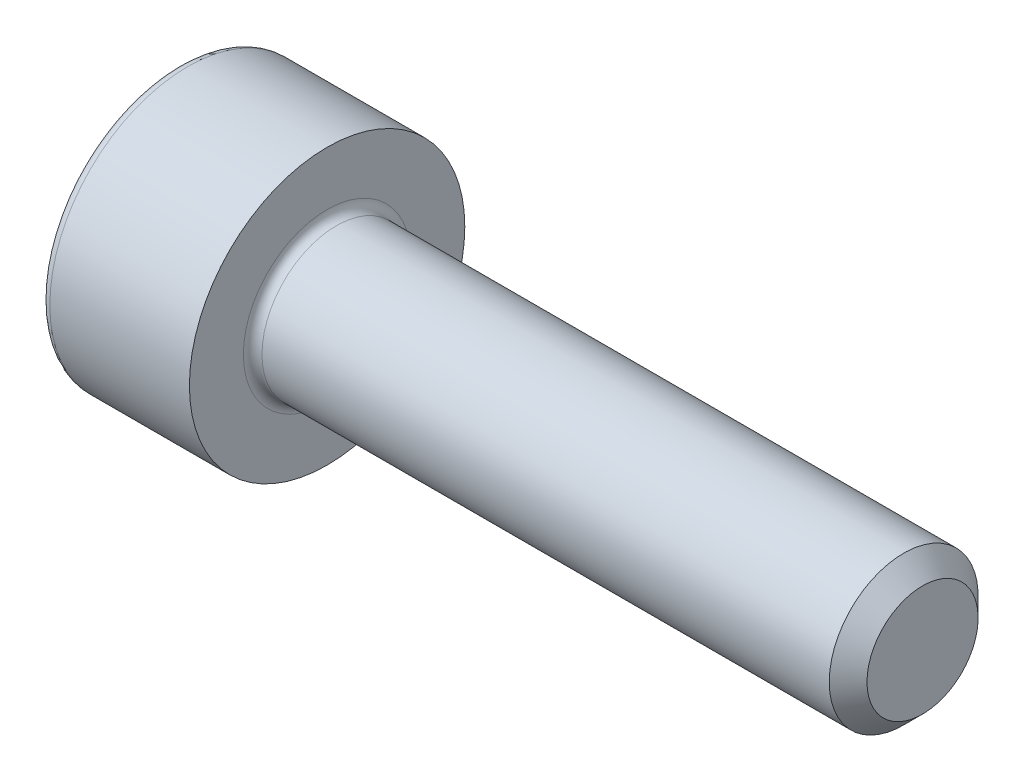
SolidWorks part; units mm, degrees
ref_plane "Front" through (0, 0, 0) normal (0, 0, 1) x (1, 0, 0)
ref_plane "Top" through (0, 0, 0) normal (0, 1, 0) x (1, 0, 0)
ref_plane "Right" through (0, 0, 0) normal (1, 0, 0) x (0, 0, -1)
sketch "Sketch1" plane through (0, 0, 0) normal (0, 0, 1) x (1, 0, 0)
  line L0 (7.7465, 1) -> (0.125, 1)
  line L1 (-2, 1.725) -> (-2, 0)
  line L2 (0, 1.85) -> (-1.875, 1.85)
  line L3 (0, 1.125) -> (0, 1.85)
  line L4 (8, 0.7465) -> (8, 0)
  line L5 (8, 0.7465) -> (7.7465, 1)
  line L6 (-2, 0) -> (0, 0) construction
  line L7 (-2, 0) -> (8, 0)
  arc A0 (-1.875, 1.85) -> (-2, 1.725) centre (-1.875, 1.725) ccw
  arc A1 (0, 1.125) -> (0.125, 1) centre (0.125, 1.125) ccw
  point P12 (0, 1.4875)
  dimension "D5" = 0.125
  dimension "D1" = 2
  dimension "D2" = 3.7
  dimension "D3" = 135
  dimension "D4" = 0.3585
  dimension "D6" = 8
  dimension "D7" = 2
revolve "Revolve1" add sketch "Sketch1" angle 360 about L7
sketch "Sketch2" plane through (-2, 0, 0) normal (-1, 0, 0) x (0, 0, 1)
  line L7 (0.75, 0.433) -> (0, 0.866)
  line L8 (0, 0.866) -> (-0.75, 0.433)
  line L9 (-0.75, 0.433) -> (-0.75, -0.433)
  line L10 (-0.75, -0.433) -> (0, -0.866)
  line L11 (0, -0.866) -> (0.75, -0.433)
  line L12 (0.75, -0.433) -> (0.75, 0.433)
  circle A0 centre (0, 0) radius 0.75 construction
  dimension "D1" = 1.5
extrude "Cut-Extrude1" cut sketch "Sketch2" against normal blind 1.1
